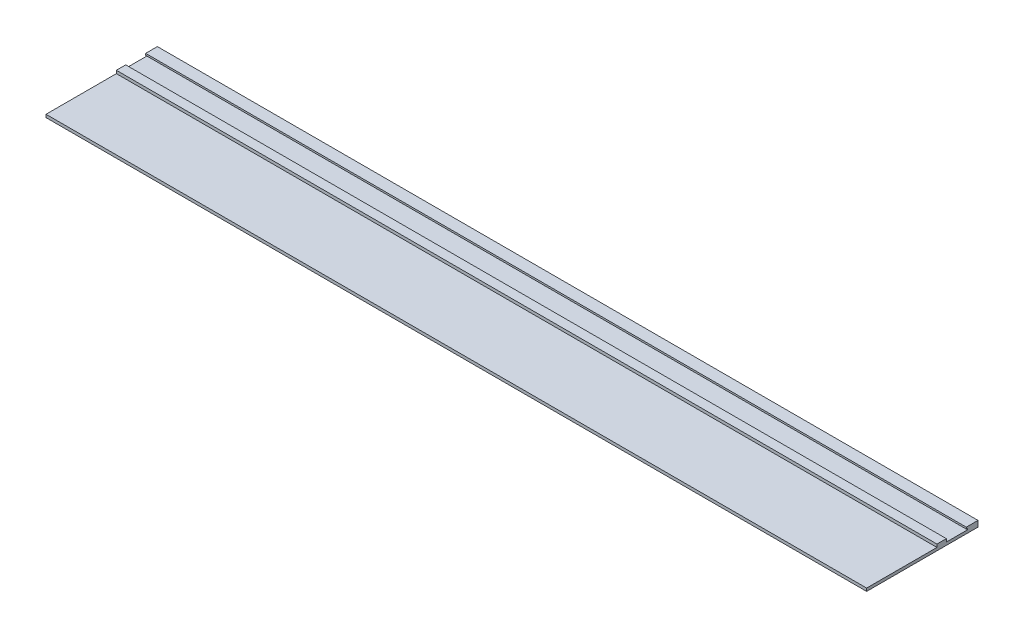
SolidWorks part; units mm, degrees
ref_plane "Спереди" through (0, 0, 0) normal (0, 0, 1) x (1, 0, 0)
ref_plane "Сверху" through (0, 0, 0) normal (0, 1, 0) x (1, 0, 0)
ref_plane "Справа" through (0, 0, 0) normal (1, 0, 0) x (0, 0, -1)
sketch "Эскиз1" plane through (0, 0, 0) normal (1, 0, 0) x (0, 0, -1)
  line L0 (0, 0) -> (190, 0)
  line L1 (190, 0) -> (190, 10)
  line L2 (190, 10) -> (170, 10)
  line L3 (170, 10) -> (170, 7.1238)
  line L4 (170, 7.1238) -> (172.0633, 7.1238)
  line L5 (172.0633, 7.1238) -> (172.0633, 4.9867)
  line L6 (172.0633, 4.9867) -> (136, 4.9867)
  line L7 (136, 4.9867) -> (136, 10)
  line L8 (136, 10) -> (120, 10)
  line L9 (120, 10) -> (120, 4.9867)
  line L10 (120, 4.9867) -> (0, 4.9867)
  line L11 (0, 4.9867) -> (0, 0)
  point P3 (66.8633, 4.9867)
  point P14 (93.2571, 0)
  point P15 (171.0994, 7.1238)
  point P16 (0, 0)
  point P17 (0, 0)
  point P18 (170.1774, 9.9733)
  point P19 (0, 0)
  point P20 (130.3754, 10.0461)
  point P21 (0, 0)
  point P22 (0, 0)
  point P23 (0, 0)
  point P24 (0, 0)
  dimension "D1" = 190
extrude "Бобышка-Вытянуть1" add sketch "Эскиз1" along normal blind 1400
